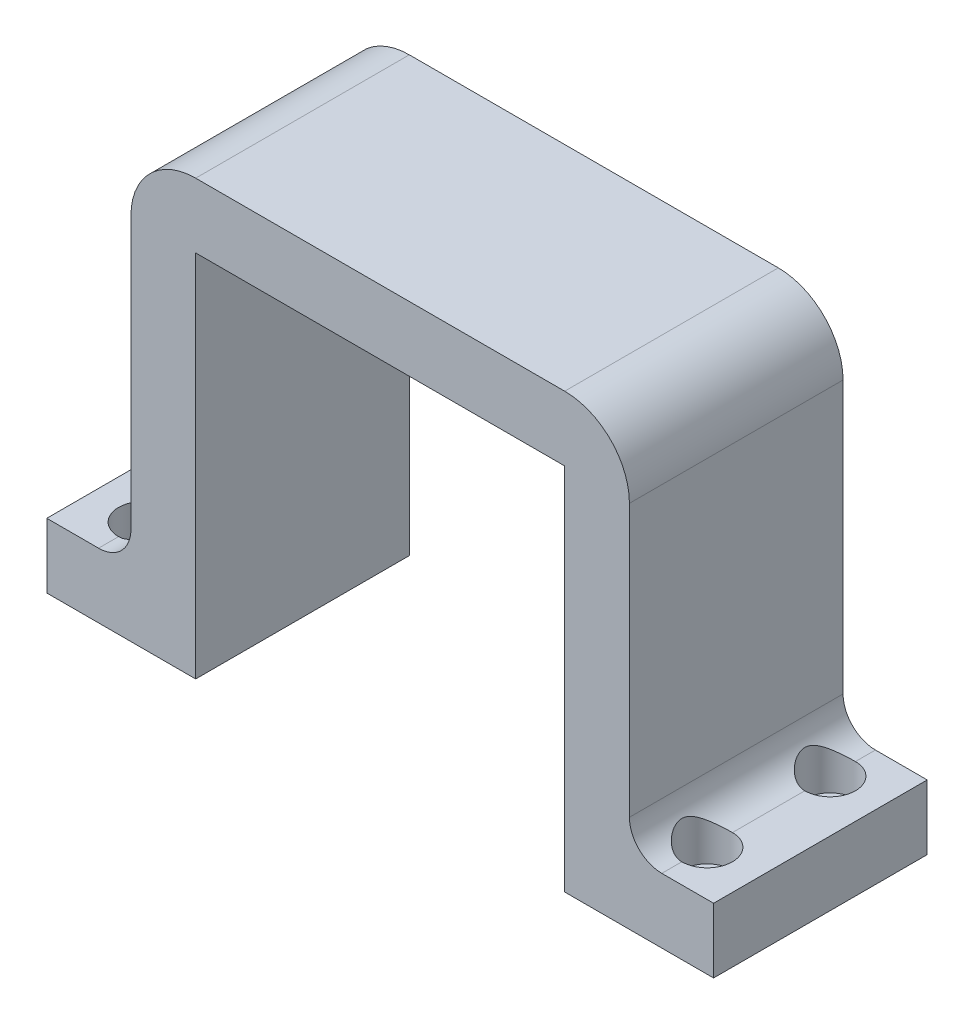
SolidWorks part; units mm, degrees
ref_plane "Front Plane" through (0, 0, 0) normal (0, 0, 1) x (1, 0, 0)
ref_plane "Top Plane" through (0, 0, 0) normal (0, 1, 0) x (1, 0, 0)
ref_plane "Right Plane" through (0, 0, 0) normal (1, 0, 0) x (0, 0, -1)
sketch "Sketch1" plane through (0, 0, 0) normal (0, 0, 1) x (1, 0, 0)
  line L0 (0, 0) -> (15, 0)
  line L1 (15, 0) -> (15, 57)
  line L2 (15, 57) -> (72, 57)
  line L3 (72, 57) -> (72, 0)
  line L4 (72, 0) -> (87, 0)
  dimension "D1" = 57
  dimension "D2" = 15
extrude "Extrude-Thin1" add sketch "Sketch1" along normal blind 33 thin thin type one direction reverse wall 10
sketch "Sketch2" plane through (0, 0, 33) normal (0, 0, 1) x (1, 0, 0)
  line L1 (0, 10) -> (-8, 10)
  line L2 (0, 10) -> (0, 0)
  line L3 (0, 0) -> (-8, 0)
  line L4 (-8, 10) -> (-8, 0)
  line L5 (87, 10) -> (95, 10)
  line L6 (87, 10) -> (87, 0)
  line L7 (87, 0) -> (95, 0)
  line L8 (95, 10) -> (95, 0)
  dimension "D1" = 8
extrude "Boss-Extrude2" add sketch "Sketch2" against normal through all contours L2 L1 L4 L3 | L6 L5 L8 L7
fillet "Fillet1" radius 10 2 edges at (82, 67, 16.5) (5, 67, 16.5)
fillet "Fillet2" radius 5 2 edges at (82, 10, 16.5) (5, 10, 16.5)
sketch "Sketch3" plane through (0, 0, 0) normal (0, -1, 0) x (1, 0, 0)
  line L0 (-8, 0) -> (-8, 33) construction
  line L1 (0, 26) -> (87, 26) construction
  line L2 (0, 26) -> (0, 7) construction
  line L3 (0, 7) -> (87, 7) construction
  line L4 (87, 26) -> (87, 7) construction
  line L5 (95, 0) -> (95, 33) construction
  line L6 (15, 33) -> (72, 33) construction
  line L7 (-8, 0) -> (15, 0) construction
  line L8 (72, 33) -> (95, 33) construction
  circle A0 centre (0, 26) radius 2
  circle A1 centre (0, 7) radius 2
  circle A2 centre (87, 26) radius 2
  circle A3 centre (87, 7) radius 2
  dimension "D1" = 4
  dimension "D2" = 8
  dimension "D3" = 8
  dimension "D4" = 7
  dimension "D5" = 7
extrude "Cut-Extrude1" cut sketch "Sketch3" against normal through all
sketch "Sketch5" plane through (0, 67, 0) normal (0, 1, 0) x (1, 0, 0)
  circle A0 centre (0, -7) radius 3.9116
  circle A1 centre (0, -26) radius 3.9116
  circle A2 centre (87, -26) radius 3.9116
  circle A3 centre (87, -7) radius 3.9116
  dimension "D1" = 7.8232
extrude "Cut-Extrude2" cut sketch "Sketch5" against normal blind 62
